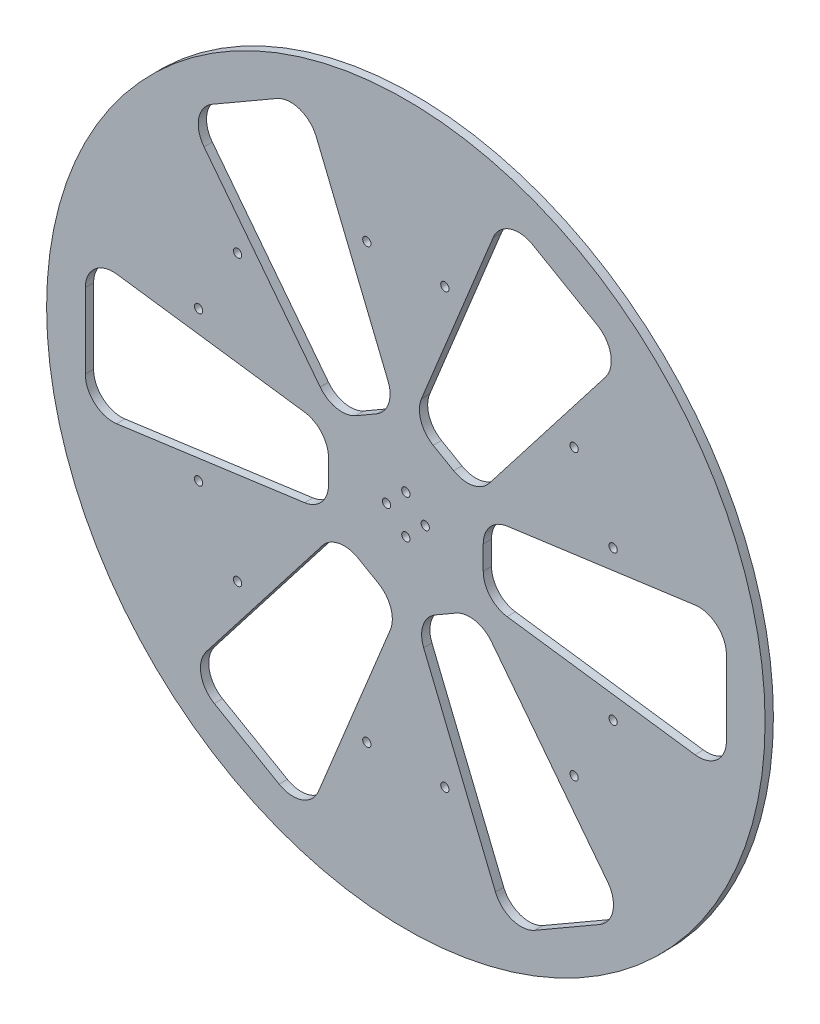
SolidWorks part; units mm, degrees
ref_plane "Front" through (0, 0, 0) normal (0, 0, 1) x (1, 0, 0)
ref_plane "Top" through (0, 0, 0) normal (0, 1, 0) x (1, 0, 0)
ref_plane "Right" through (0, 0, 0) normal (1, 0, 0) x (0, 0, -1)
sketch "草图1" plane through (0, 0, 0) normal (0, 0, 1) x (1, 0, 0)
  line L12 (-14.4007, 24.0129) -> (-18.0996, 21.8773)
  line L20 (-14.4007, 24.0129) -> (-10.7019, 26.1484)
  line L21 (-27.9961, -0.465) -> (-27.9961, -4.7361)
  line L22 (-27.9961, -0.465) -> (-27.9961, 3.8061)
  line L23 (-70.13, 93.4512) -> (-46.6715, 106.995)
  line L24 (-115.9961, -14.0088) -> (-115.9961, 13.0788)
  line L25 (-36.645, -14.6444) -> (-104.645, -23.9171)
  line L26 (-36.645, 13.7144) -> (-104.645, 22.9872)
  line L27 (-31.0049, 24.4133) -> (-73.0353, 78.6667)
  line L28 (-6.4455, 38.5927) -> (-32.415, 102.1188)
  line L29 (13.5954, 24.4779) -> (9.8965, 26.6134)
  line L30 (13.5954, 24.4779) -> (17.2943, 22.3423)
  line L31 (45.8661, 107.46) -> (69.3247, 93.9162)
  line L32 (5.6401, 39.0577) -> (31.6097, 102.5838)
  line L33 (30.1995, 24.8783) -> (72.23, 79.1317)
  line L34 (27.9961, 0.465) -> (27.9961, 4.7361)
  line L35 (27.9961, 0.465) -> (27.9961, -3.8061)
  line L36 (115.9961, 14.0088) -> (115.9961, -13.0788)
  line L37 (36.645, 14.6444) -> (104.645, 23.9171)
  line L38 (36.645, -13.7144) -> (104.645, -22.9872)
  line L39 (14.4007, -24.0129) -> (18.0996, -21.8773)
  line L40 (14.4007, -24.0129) -> (10.7019, -26.1484)
  line L41 (70.13, -93.4512) -> (46.6715, -106.995)
  line L42 (31.0049, -24.4133) -> (73.0353, -78.6667)
  line L43 (6.4455, -38.5927) -> (32.415, -102.1188)
  line L44 (-13.5954, -24.4779) -> (-9.8965, -26.6134)
  line L45 (-13.5954, -24.4779) -> (-17.2943, -22.3423)
  line L46 (-45.8661, -107.46) -> (-69.3247, -93.9162)
  line L47 (-5.6401, -39.0577) -> (-31.6097, -102.5838)
  line L48 (-30.1995, -24.8783) -> (-72.23, -79.1317)
  circle A0 centre (0, 0) radius 130
  arc A1 (-36.645, -14.6444) -> (-27.9961, -4.7361) centre (-37.9961, -4.7361) ccw
  arc A2 (-27.9961, 3.8061) -> (-36.645, 13.7144) centre (-37.9961, 3.8061) ccw
  arc A3 (-115.9961, 13.0788) -> (-104.645, 22.9872) centre (-105.9961, 13.0788) cw
  arc A4 (-104.645, -23.9171) -> (-115.9961, -14.0088) centre (-105.9961, -14.0088) cw
  arc A5 (-31.0049, 24.4133) -> (-18.0996, 21.8773) centre (-23.0996, 30.5376) ccw
  arc A6 (-10.7019, 26.1484) -> (-6.4455, 38.5927) centre (-15.7019, 34.8087) ccw
  arc A7 (-46.6715, 106.995) -> (-32.415, 102.1188) centre (-41.6715, 98.3348) cw
  arc A8 (-73.0353, 78.6667) -> (-70.13, 93.4512) centre (-65.13, 84.791) cw
  arc A9 (5.6401, 39.0577) -> (9.8965, 26.6134) centre (14.8965, 35.2737) ccw
  arc A10 (17.2943, 22.3423) -> (30.1995, 24.8783) centre (22.2943, 31.0026) ccw
  arc A11 (69.3247, 93.9162) -> (72.23, 79.1317) centre (64.3247, 85.2559) cw
  arc A12 (31.6097, 102.5838) -> (45.8661, 107.46) centre (40.8661, 98.7997) cw
  arc A13 (36.645, 14.6444) -> (27.9961, 4.7361) centre (37.9961, 4.7361) ccw
  arc A14 (27.9961, -3.8061) -> (36.645, -13.7144) centre (37.9961, -3.8061) ccw
  arc A15 (115.9961, -13.0788) -> (104.645, -22.9872) centre (105.9961, -13.0788) cw
  arc A16 (104.645, 23.9171) -> (115.9961, 14.0088) centre (105.9961, 14.0088) cw
  arc A17 (31.0049, -24.4133) -> (18.0996, -21.8773) centre (23.0996, -30.5376) ccw
  arc A18 (10.7019, -26.1484) -> (6.4455, -38.5927) centre (15.7019, -34.8087) ccw
  arc A19 (46.6715, -106.995) -> (32.415, -102.1188) centre (41.6715, -98.3348) cw
  arc A20 (73.0353, -78.6667) -> (70.13, -93.4512) centre (65.13, -84.791) cw
  arc A21 (-5.6401, -39.0577) -> (-9.8965, -26.6134) centre (-14.8965, -35.2737) ccw
  arc A22 (-17.2943, -22.3423) -> (-30.1995, -24.8783) centre (-22.2943, -31.0026) ccw
  arc A23 (-69.3247, -93.9162) -> (-72.23, -79.1317) centre (-64.3247, -85.2559) cw
  arc A24 (-31.6097, -102.5838) -> (-45.8661, -107.46) centre (-40.8661, -98.7997) cw
  circle A25 centre (-7, 0) radius 1.5
  circle A26 centre (0, 7) radius 1.5
  circle A27 centre (7, 0) radius 1.5
  circle A28 centre (0, -7) radius 1.5
  circle A29 centre (-75, -27) radius 1.5
  circle A30 centre (-75, 27) radius 1.5
  circle A31 centre (-60.8827, 51.4519) radius 1.5
  circle A32 centre (-14.1173, 78.4519) radius 1.5
  circle A33 centre (14.1173, 78.4519) radius 1.5
  circle A34 centre (60.8827, 51.4519) radius 1.5
  circle A35 centre (75, 27) radius 1.5
  circle A36 centre (75, -27) radius 1.5
  circle A37 centre (60.8827, -51.4519) radius 1.5
  circle A38 centre (14.1173, -78.4519) radius 1.5
  circle A39 centre (-14.1173, -78.4519) radius 1.5
  circle A40 centre (-60.8827, -51.4519) radius 1.5
  point P84 (0, 0)
  point P93 (0, 0)
  dimension "D1" = 10
  dimension "D2" = 6
  dimension "D3" = 7
  dimension "D4" = 4
extrude "凸台-拉伸2" add sketch "草图1" along normal blind 3
